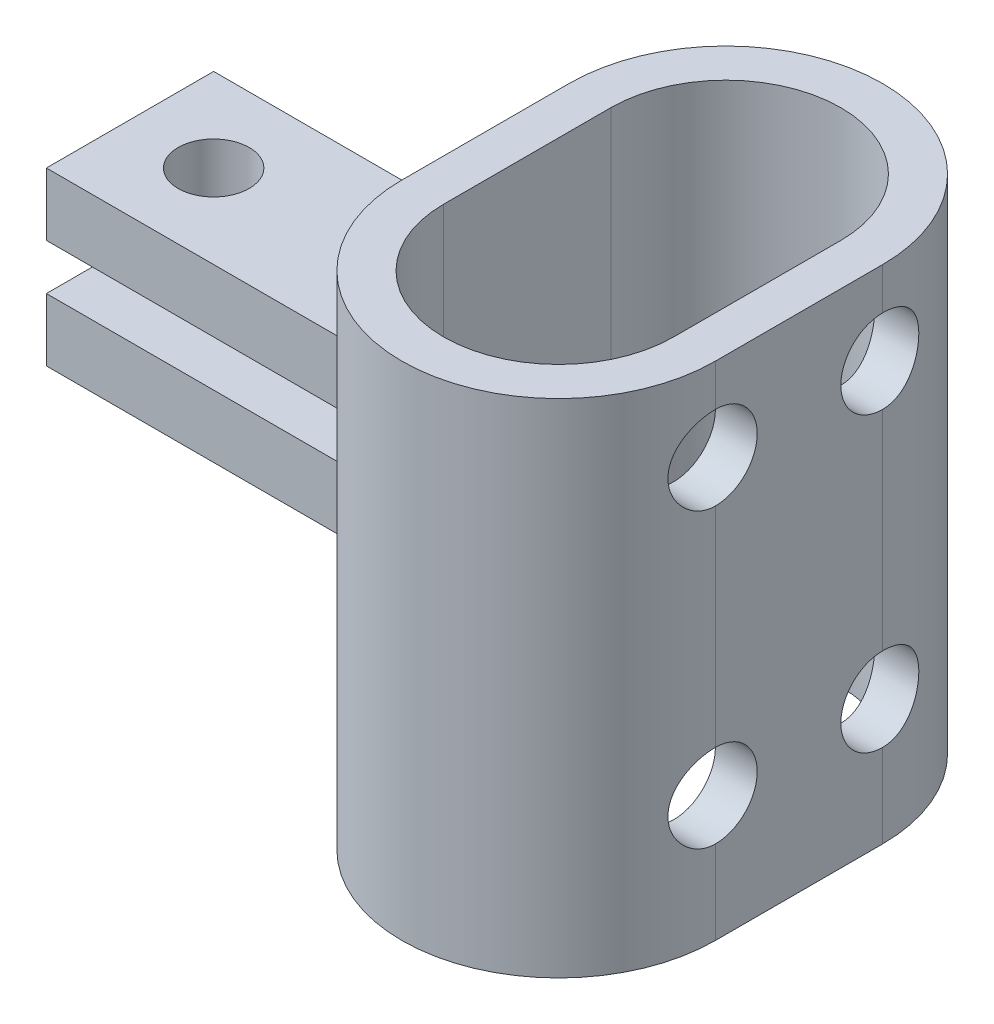
SolidWorks part; units mm, degrees
ref_plane "Front Plane" through (0, 0, 0) normal (0, 0, 1) x (1, 0, 0)
ref_plane "Top Plane" through (0, 0, 0) normal (0, 1, 0) x (1, 0, 0)
ref_plane "Right Plane" through (0, 0, 0) normal (1, 0, 0) x (0, 0, -1)
sketch "Sketch1" plane through (0, 0, 0) normal (0, 1, 0) x (1, 0, 0)
  line L1 (-4, 4) -> (4, 4)
  line L2 (-4, 4) -> (-4, -4)
  line L3 (-4, -4) -> (4, -4)
  line L4 (4, 4) -> (4, -4)
  line L5 (-4, 4) -> (4, -4) construction
  line L6 (-4, -4) -> (4, 4) construction
  line L7 (4, 4) -> (10, 4)
  line L9 (4, -4) -> (10, -4)
  line L10 (10, 4) -> (10, -4)
  circle A0 centre (0, 0) radius 1.7
  dimension "D1" = 3.4
  dimension "D2" = 8
  dimension "D3" = 8
  dimension "D4" = 10
extrude "Boss-Extrude1" add sketch "Sketch1" along normal blind 3 contours L10 L7 L4 L9 | L4 L1 L2 L3 A0
sketch "Sketch2" plane through (10, 0, 0) normal (1, 0, 0) x (0, 0, -1)
  line L0 (4.4, 0) -> (-4.4, 0) construction
  line L1 (-4, 3) -> (4, 3)
  line L2 (-4, 3) -> (-4, -1.1)
  line L3 (-4, -1.1) -> (4, -1.1)
  line L4 (4, 3) -> (4, -1.1)
  dimension "D1" = 1.1
extrude "Boss-Extrude2" add sketch "Sketch2" along normal blind 3
mirror "Mirror1" about plane through (13, -1.1, 4) normal (0, 1, 0) of bodies 107
sketch "Sketch3" plane through (0, 3, 0) normal (0, 1, 0) x (1, 0, 0)
  line L0 (20.5, 4) -> (20.5, -4) construction
  line L5 (28, 4) -> (28, -4)
  line L6 (13, 4) -> (13, -4)
  line L7 (13, 4) -> (13, -4) construction
  line L8 (-4, -4) -> (13, -4) construction
  line L9 (20.5, 4) -> (20.5, -4) construction
  line L10 (26, 4) -> (26, -4)
  line L11 (15, 4) -> (15, -4)
  arc A2 (28, 4) -> (13, 4) centre (20.5, 4) ccw
  arc A3 (13, -4) -> (28, -4) centre (20.5, -4) ccw
  arc A4 (26, 4) -> (15, 4) centre (20.5, 4) ccw
  arc A5 (15, -4) -> (26, -4) centre (20.5, -4) ccw
  point P2 (20.5, 0)
  point P9 (20.5, 0)
  dimension "D1" = 7.5
  dimension "D2" = 7.5
  dimension "D3" = 8
  dimension "D4" = 2
extrude "Boss-Extrude3" add sketch "Sketch3" along normal blind 8 and the other way blind 16
sketch "Sketch4" plane through (28, 0, 0) normal (1, 0, 0) x (0, 0, -1)
  line L0 (-4, 11) -> (-11.5, 11) construction
  line L1 (0, 13.2) -> (0, -13.2) construction
  line L3 (12.65, 0) -> (-12.65, 0) construction
  circle A0 centre (-4, 7) radius 2
  circle A1 centre (4, 7) radius 2
  circle A2 centre (4, -7) radius 2
  circle A3 centre (-4, -7) radius 2
  point P2 (-1.9697, 8.2574)
  point P3 (-5.6195, 8.0101)
  dimension "D1" = 4
  dimension "D2" = 4
  dimension "D3" = 4
extrude "Cut-Extrude1" cut sketch "Sketch4" against normal blind 8
